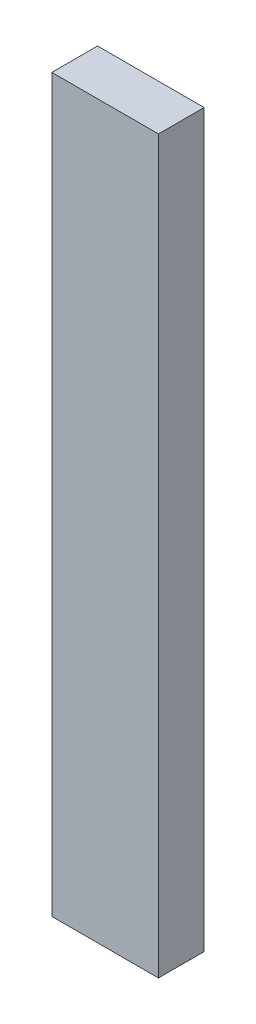
SolidWorks part; units mm, degrees
material "Oak"
ref_plane "Front Plane" through (0, 0, 0) normal (0, 0, 1) x (1, 0, 0)
ref_plane "Top Plane" through (0, 0, 0) normal (0, 1, 0) x (1, 0, 0)
ref_plane "Right Plane" through (0, 0, 0) normal (1, 0, 0) x (0, 0, -1)
sketch "Sketch1" plane through (0, 0, 0) normal (0, 1, 0) x (1, 0, 0)
  line L1 (-44.45, -19.05) -> (44.45, -19.05)
  line L2 (-44.45, -19.05) -> (-44.45, 19.05)
  line L3 (-44.45, 19.05) -> (44.45, 19.05)
  line L4 (44.45, -19.05) -> (44.45, 19.05)
  line L5 (-44.45, -19.05) -> (44.45, 19.05) construction
  line L6 (-44.45, 19.05) -> (44.45, -19.05) construction
  point P0 (0, 0)
  dimension "D1" = 38.1
  dimension "D2" = 88.9
extrude "Boss-Extrude1" add sketch "Sketch1" along normal blind 609.6 contours L3 L4 L1 L2
